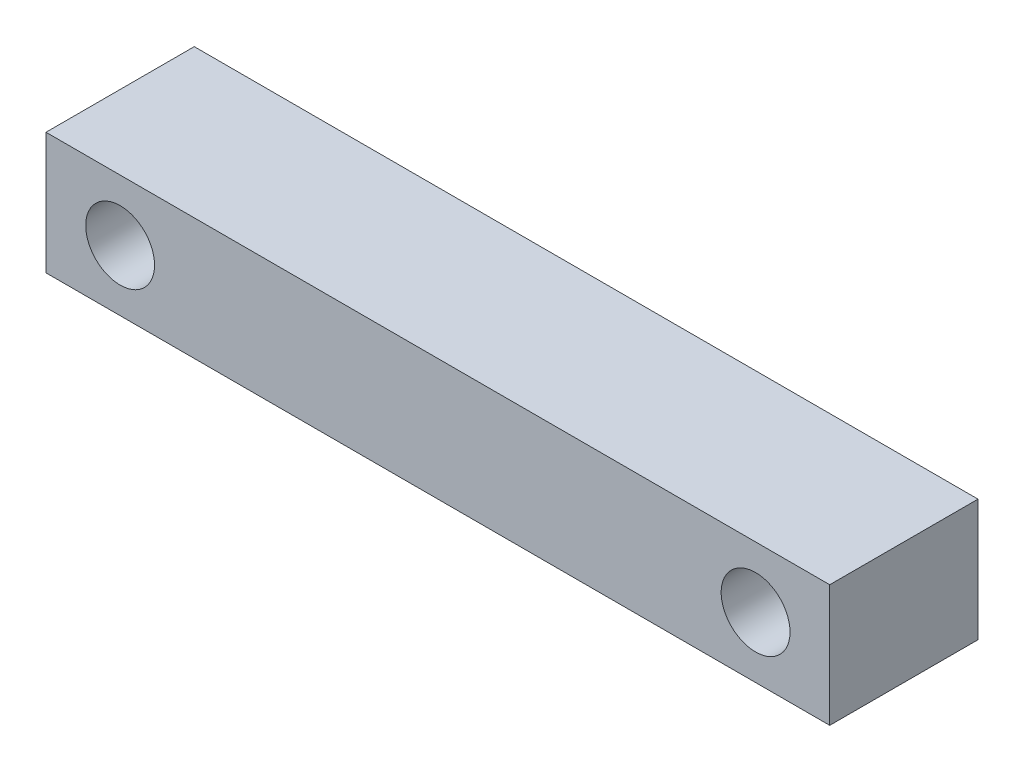
SolidWorks part; units mm, degrees
ref_plane "Front Plane" through (0, 0, 0) normal (0, 0, 1) x (1, 0, 0)
ref_plane "Top Plane" through (0, 0, 0) normal (0, 1, 0) x (1, 0, 0)
ref_plane "Right Plane" through (0, 0, 0) normal (1, 0, 0) x (0, 0, -1)
sketch "Sketch1" plane through (0, 0, 0) normal (0, 0, 1) x (1, 0, 0)
  line L1 (-148, 0) -> (148, 0)
  line L2 (-148, 0) -> (-148, -46)
  line L3 (-148, -46) -> (148, -46)
  line L4 (148, 0) -> (148, -46)
  circle A0 centre (-120, -23) radius 13 construction
  circle A1 centre (-120, -23) radius 13
  circle A2 centre (120, -23) radius 13 construction
  circle A3 centre (120, -23) radius 13
  dimension "D1" = 46
extrude "Extrude1" add sketch "Sketch1" along normal blind 56
